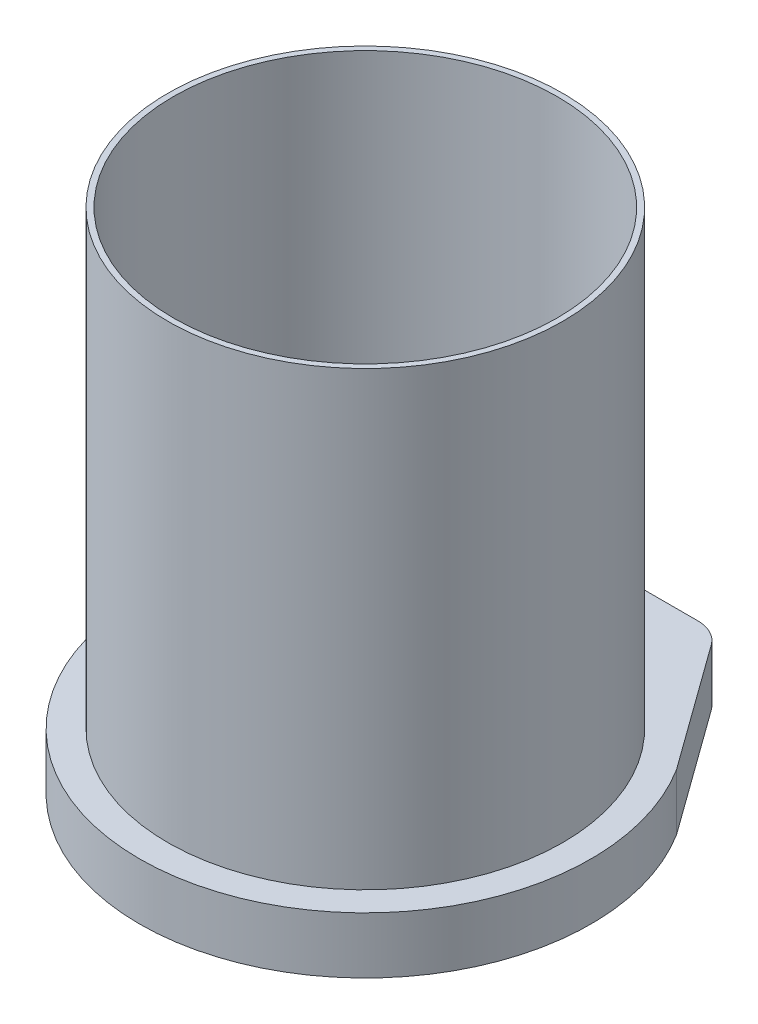
SolidWorks part; units mm, degrees
ref_plane "Спереди" through (0, 0, 0) normal (0, 0, 1) x (1, 0, 0)
ref_plane "Сверху" through (0, 0, 0) normal (0, 1, 0) x (1, 0, 0)
ref_plane "Справа" through (0, 0, 0) normal (1, 0, 0) x (0, 0, -1)
sketch "Эскиз1" plane through (0, 0, 0) normal (0, 1, 0) x (1, 0, 0)
  circle A0 centre (0, 0) radius 170
extrude "Вытянуть-Тонкостенный1" add sketch "Эскиз1" along normal blind 400 thin
sketch "Эскиз2" plane through (0, 0, 0) normal (0, -1, 0) x (1, 0, 0)
  line L0 (-64.6743, -230) -> (64.6678, -230)
  line L1 (88.9815, -217.5739) -> (169.425, -106.2787)
  line L2 (-168.9828, -106.9804) -> (-88.982, -217.5823)
  arc A0 (-168.9828, -106.9804) -> (169.425, -106.2787) centre (0, 0) cw
  arc A1 (64.6678, -230) -> (88.9815, -217.5739) centre (64.6678, -200) ccw
  arc A2 (-64.6743, -230) -> (-88.982, -217.5823) centre (-64.6743, -200) cw
  dimension "D1" = 30
extrude "Бобышка-Вытянуть1" add sketch "Эскиз2" along normal blind 50
